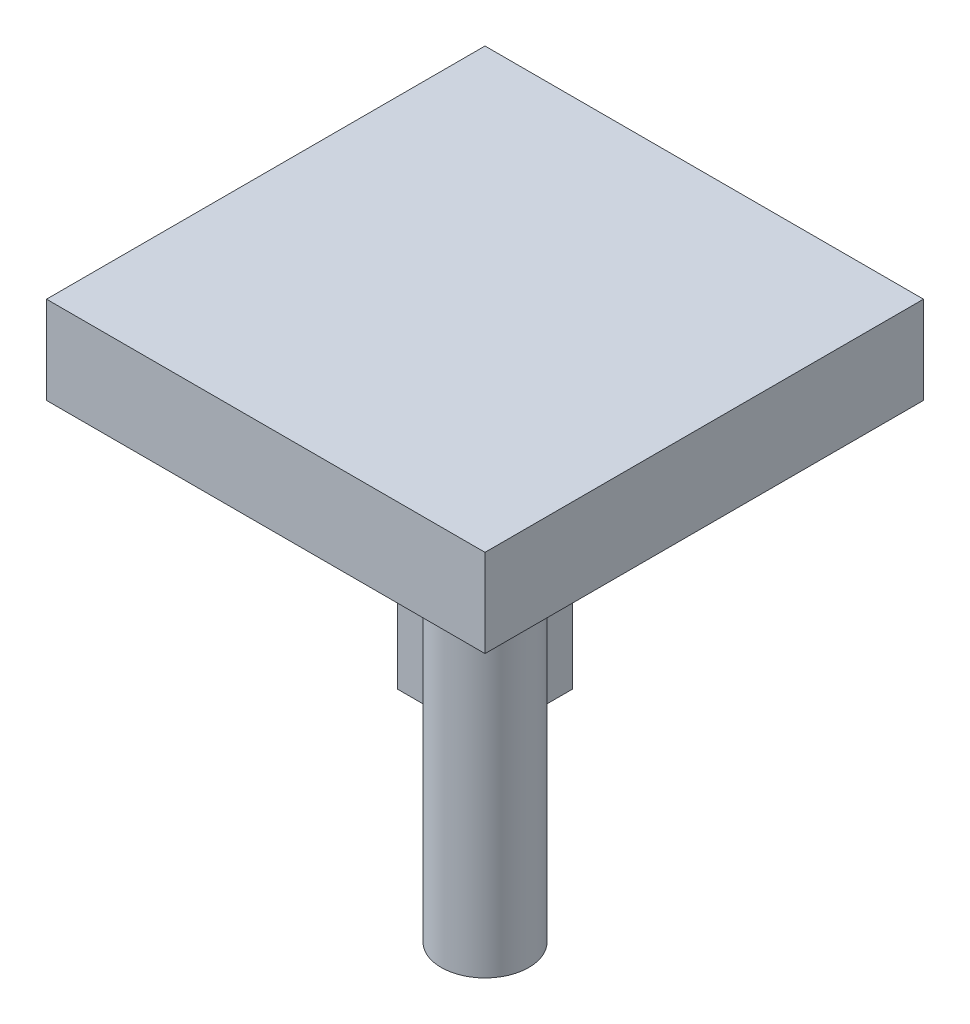
SolidWorks part; units mm, degrees
ref_plane "Front Plane" through (0, 0, 0) normal (0, 0, 1) x (1, 0, 0)
ref_plane "Top Plane" through (0, 0, 0) normal (0, 1, 0) x (1, 0, 0)
ref_plane "Right Plane" through (0, 0, 0) normal (1, 0, 0) x (0, 0, -1)
sketch "Sketch1" plane through (0, 0, 0) normal (0, 1, 0) x (1, 0, 0)
  line L1 (50, 50) -> (-50, 50)
  line L2 (50, 50) -> (50, -50)
  line L3 (50, -50) -> (-50, -50)
  line L4 (-50, 50) -> (-50, -50)
  line L5 (50, 50) -> (-50, -50) construction
  line L6 (50, -50) -> (-50, 50) construction
  point P0 (0, 0)
  dimension "D1" = 100
extrude "Boss-Extrude1" add sketch "Sketch1" along normal blind 20
sketch "Sketch2" plane through (0, 0, 0) normal (0, -1, 0) x (1, 0, 0)
  line L0 (50, 50) -> (0, 0) construction
  line L1 (0, 0) -> (-50, -50) construction
  line L3 (-35, -35) -> (-15, -35)
  line L4 (-35, -35) -> (-35, -15)
  line L5 (-35, -15) -> (-15, -15)
  line L6 (-15, -35) -> (-15, -15)
  line L7 (-35, -35) -> (-15, -15) construction
  line L8 (-35, -15) -> (-15, -35) construction
  circle A0 centre (25, 25) radius 10
  point P8 (-25, -25)
  point P13 (0, 0)
  point P14 (0, 0)
  dimension "D1" = 20
  dimension "D2" = 20
surface "Surface-Extrude1" sketch "Sketch2" parameters "D1"=80, "D19"=2
